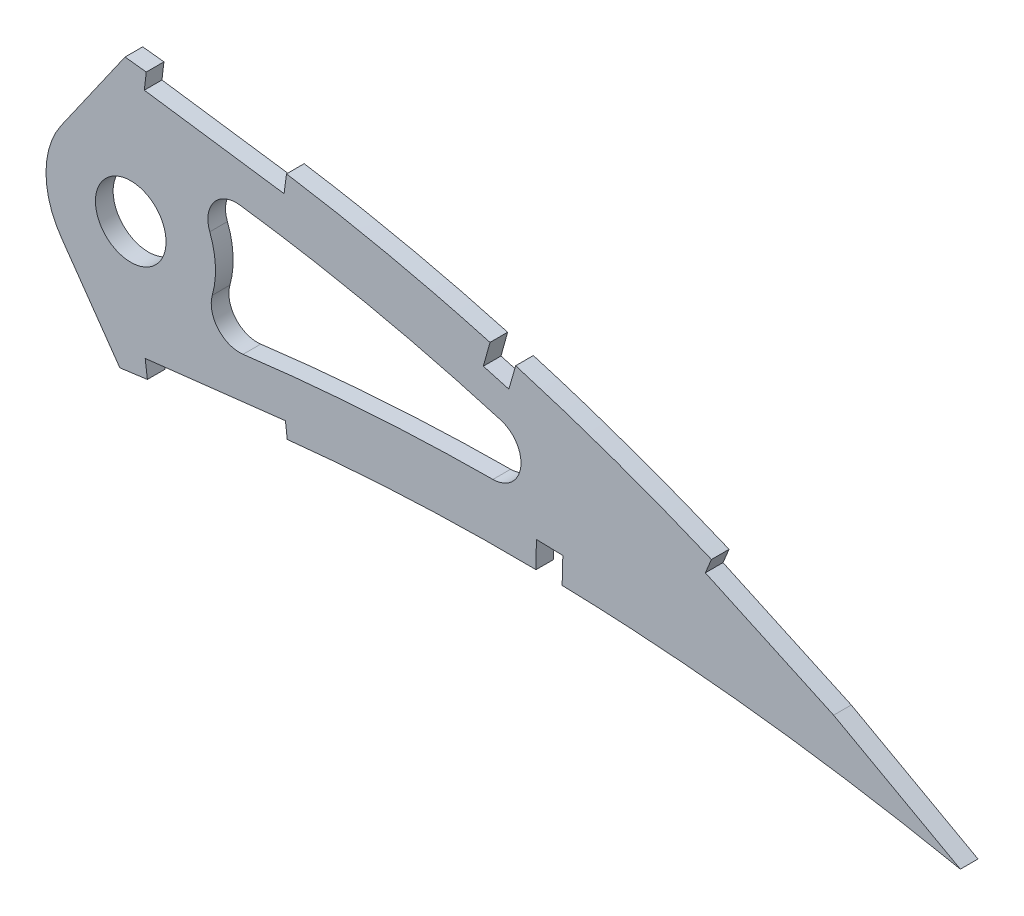
SolidWorks part; units mm, degrees
ref_plane "Front Plane" through (0, 0, 0) normal (0, 0, 1) x (1, 0, 0)
ref_plane "Top Plane" through (0, 0, 0) normal (0, 1, 0) x (1, 0, 0)
ref_plane "Right Plane" through (0, 0, 0) normal (1, 0, 0) x (0, 0, -1)
curve "Curve1"
  spline degree 3 poles (452.1031, 0.7048, 0) (452.0685, 0.7262, 0) (451.9301, 0.8117, 0) (451.6183, 1.003, 0) (451.099, 1.3216, 0) (450.372, 1.7653, 0) (449.438, 2.3329, 0) (448.2963, 3.0204, 0) (446.9478, 3.8257, 0) (445.3928, 4.7448, 0) (443.6314, 5.7736, 0) (441.6643, 6.9077, 0) (439.4916, 8.1409, 0) (437.1143, 9.468, 0) (434.5331, 10.8828, 0) (431.7485, 12.3789, 0) (428.7615, 13.9486, 0) (425.5733, 15.5853, 0) (422.1844, 17.2798, 0) (418.5964, 19.0251, 0) (414.8106, 20.8125, 0) (410.8282, 22.6325, 0) (406.6515, 24.4776, 0) (402.2816, 26.3365, 0) (397.7212, 28.201, 0) (392.972, 30.0605, 0) (388.0369, 31.9065, 0) (382.9178, 33.7272, 0) (377.6186, 35.5144, 0) (372.1418, 37.2567, 0) (366.4913, 38.9446, 0) (360.6704, 40.5671, 0) (354.684, 42.1159, 0) (348.5359, 43.5797, 0) (342.2312, 44.9487, 0) (335.775, 46.2147, 0) (329.1727, 47.3651, 0) (322.4425, 48.3989, 0) (315.6929, 49.2588, 0) (308.9571, 50.1023, 0) (302.2314, 50.8946, 0) (295.4235, 51.6533, 0) (288.5399, 52.3742, 0) (281.5875, 53.055, 0) (274.5733, 53.6928, 0) (267.5046, 54.2857, 0) (260.3883, 54.8303, 0) (253.2318, 55.3259, 0) (246.0422, 55.768, 0) (238.8272, 56.1563, 0) (231.5941, 56.4881, 0) (224.3504, 56.7611, 0) (217.1039, 56.9737, 0) (209.862, 57.1238, 0) (202.6326, 57.2105, 0) (195.4232, 57.2315, 0) (188.2416, 57.1863, 0) (181.0954, 57.0734, 0) (173.9924, 56.8912, 0) (166.9401, 56.6395, 0) (159.9462, 56.3182, 0) (153.0184, 55.9248, 0) (146.164, 55.4618, 0) (139.3909, 54.9271, 0) (132.7063, 54.3206, 0) (126.1174, 53.645, 0) (119.6314, 52.8983, 0) (113.2554, 52.0826, 0) (106.9962, 51.1996, 0) (100.8609, 50.2488, 0) (94.8561, 49.2329, 0) (88.9882, 48.153, 0) (83.2635, 47.0122, 0) (77.6882, 45.8109, 0) (72.2682, 44.5525, 0) (67.0092, 43.2395, 0) (61.9167, 41.874, 0) (56.9959, 40.4594, 0) (52.2519, 38.999, 0) (47.6902, 37.4943, 0) (43.3141, 35.951, 0) (39.1291, 34.3702, 0) (35.1384, 32.7568, 0) (31.3466, 31.113, 0) (27.7567, 29.4439, 0) (24.3726, 27.7512, 0) (21.1967, 26.0397, 0) (18.2324, 24.3122, 0) (15.4823, 22.5717, 0) (12.9477, 20.8227, 0) (10.632, 19.0664, 0) (8.5361, 17.307, 0) (6.6613, 15.5474, 0) (5.0102, 13.7886, 0) (3.5829, 12.0339, 0) (2.3811, 10.2847, 0) (1.4051, 8.5424, 0) (0.6571, 6.8085, 0) (0.1363, 5.084, 0) (-0.1488, 3.3712, 0) (-0.2197, 1.669, 0) (-0.0731, 0.5555, 0) (0, 0, 0) knots 0 0 0 0 0.000254 0.001015 0.002283 0.004057 0.006331 0.009105 0.012374 0.016134 0.02038 0.025106 0.030306 0.035972 0.0421 0.048678 0.055702 0.06316 0.071046 0.07935 0.088063 0.097176 0.106678 0.116562 0.126814 0.137428 0.148394 0.1597 0.171338 0.183298 0.19557 0.208144 0.221012 0.234162 0.247587 0.261277 0.275223 0.289414 0.303771 0.317689 0.331784 0.34604 0.360444 0.374983 0.38964 0.404403 0.419257 0.434187 0.449177 0.464215 0.479284 0.49437 0.509458 0.524532 0.539579 0.554583 0.56953 0.584403 0.599191 0.613877 0.628447 0.642889 0.657186 0.671326 0.685294 0.699078 0.712665 0.726043 0.739198 0.752118 0.764792 0.777208 0.789356 0.801224 0.812804 0.824083 0.835055 0.84571 0.856038 0.866034 0.875689 0.884998 0.893953 0.902553 0.910789 0.918661 0.926166 0.933303 0.940071 0.946475 0.952518 0.958205 0.963547 0.968557 0.97325 0.977651 0.981787 0.985694 0.989415 0.993001 0.996508 1 1 1 1
curve "Curve2"
  spline degree 3 poles (0, 0, 0) (0.1161, -0.5481, 0) (0.3488, -1.6467, 0) (0.9811, -3.2283, 0) (1.8173, -4.7487, 0) (2.8749, -6.2038, 0) (4.147, -7.5932, 0) (5.6306, -8.9184, 0) (7.3243, -10.1787, 0) (9.226, -11.3735, 0) (11.3328, -12.5041, 0) (13.6425, -13.5697, 0) (16.1528, -14.5701, 0) (18.8611, -15.5039, 0) (21.764, -16.3724, 0) (24.8588, -17.1737, 0) (28.1419, -17.9088, 0) (31.6103, -18.5759, 0) (35.26, -19.1755, 0) (39.0874, -19.7075, 0) (43.0885, -20.172, 0) (47.2594, -20.5682, 0) (51.596, -20.8969, 0) (56.0938, -21.1583, 0) (60.7487, -21.3533, 0) (65.556, -21.481, 0) (70.5112, -21.5436, 0) (75.6096, -21.5419, 0) (80.8464, -21.4754, 0) (86.2171, -21.3479, 0) (91.7164, -21.1586, 0) (97.3395, -20.9096, 0) (103.0813, -20.6036, 0) (108.9365, -20.2416, 0) (114.9002, -19.8251, 0) (120.967, -19.3576, 0) (127.1315, -18.8401, 0) (133.3883, -18.2757, 0) (139.7319, -17.6673, 0) (146.1567, -17.0167, 0) (152.6572, -16.327, 0) (159.2275, -15.6004, 0) (165.862, -14.8409, 0) (172.5546, -14.0497, 0) (179.2998, -13.2315, 0) (186.0911, -12.3877, 0) (192.923, -11.5217, 0) (199.7891, -10.6375, 0) (206.6832, -9.7349, 0) (213.5994, -8.8205, 0) (220.5311, -7.8935, 0) (227.4721, -6.9586, 0) (234.4161, -6.0188, 0) (241.3564, -5.0743, 0) (248.2868, -4.1291, 0) (255.2009, -3.1857, 0) (262.0918, -2.2442, 0) (268.9535, -1.3094, 0) (275.779, -0.3811, 0) (282.5619, 0.5389, 0) (289.2958, 1.4477, 0) (295.9744, 2.3443, 0) (302.5907, 3.228, 0) (309.138, 4.0992, 0) (315.5119, 4.9314, 0) (321.6955, 5.769, 0) (327.7099, 6.4556, 0) (333.6493, 7.0417, 0) (339.52, 7.5222, 0) (345.315, 7.9041, 0) (351.0275, 8.19, 0) (356.6509, 8.3839, 0) (362.1779, 8.4917, 0) (367.6017, 8.516, 0) (372.9148, 8.4647, 0) (378.1105, 8.3417, 0) (383.1813, 8.1528, 0) (388.1203, 7.9042, 0) (392.9205, 7.6027, 0) (397.5745, 7.2527, 0) (402.076, 6.8625, 0) (406.4179, 6.4377, 0) (410.5937, 5.9833, 0) (414.5972, 5.5086, 0) (418.4221, 5.0169, 0) (422.0625, 4.5163, 0) (425.5126, 4.0117, 0) (428.7669, 3.5097, 0) (431.8204, 3.015, 0) (434.6681, 2.5342, 0) (437.3055, 2.0718, 0) (439.7281, 1.6323, 0) (441.9324, 1.2212, 0) (443.9143, 0.8406, 0) (445.6709, 0.4968, 0) (447.199, 0.1913, 0) (448.4964, -0.0716, 0) (449.5609, -0.2909, 0) (450.3908, -0.463, 0) (450.9844, -0.5881, 0) (451.3411, -0.6626, 0) (451.4997, -0.6964, 0) (451.5393, -0.7048, 0) knots 0 0 0 0 0.003638 0.007293 0.011028 0.014901 0.018963 0.023258 0.027821 0.032679 0.037853 0.043362 0.049215 0.055422 0.061989 0.068918 0.076211 0.083868 0.091887 0.100266 0.109 0.118085 0.127515 0.137285 0.147388 0.157816 0.168563 0.179619 0.190977 0.202627 0.21456 0.226767 0.239236 0.251959 0.264924 0.27812 0.291536 0.30516 0.318981 0.332985 0.347163 0.361499 0.375981 0.390597 0.405333 0.420175 0.43511 0.450124 0.465203 0.480333 0.495501 0.51069 0.525887 0.541078 0.556247 0.571382 0.586466 0.601485 0.616424 0.631269 0.646007 0.660621 0.675098 0.689423 0.703582 0.716908 0.730009 0.742952 0.755726 0.76832 0.780724 0.792927 0.804916 0.816679 0.828204 0.839475 0.850481 0.861208 0.871639 0.881763 0.891564 0.901027 0.910139 0.918884 0.927249 0.935221 0.942785 0.949928 0.956638 0.962904 0.968712 0.974054 0.978918 0.983297 0.98718 0.990561 0.993433 0.995791 0.99763 0.998946 0.999737 1 1 1 1
sketch "Sketch1" plane through (0, 0, 0) normal (0, 0, 1) x (1, 0, 0)
  line L24 (452.1031, 0.7048) -> (456.094, -1.6764)
  line L25 (451.5393, -0.7048) -> (456.094, -1.6764)
  spline S2 degree 3 poles (-3866.0233, -1022.3851) (78.0891, 72.3921) (-8.7669, 21.1547) (0.9811, -3.2283) (1.8173, -4.7487) (2.8749, -6.2038) (4.147, -7.5932) (5.6306, -8.9184) (7.3243, -10.1787) (9.226, -11.3735) (11.3328, -12.5041) (13.6425, -13.5697) (16.1528, -14.5701) (18.8611, -15.5039) (21.764, -16.3724) (24.8588, -17.1737) (28.1419, -17.9088) (31.6103, -18.5759) (35.26, -19.1755) (39.0874, -19.7075) (43.0885, -20.172) (47.2594, -20.5682) (51.596, -20.8969) (56.0938, -21.1583) (60.7487, -21.3533) (65.556, -21.481) (70.5112, -21.5436) (75.6096, -21.5419) (80.8464, -21.4754) (86.2171, -21.3479) (91.7164, -21.1586) (97.3395, -20.9096) (103.0813, -20.6036) (108.9365, -20.2416) (114.9002, -19.8251) (120.967, -19.3576) (127.1315, -18.8401) (133.3883, -18.2757) (139.7319, -17.6673) (146.1567, -17.0167) (152.6572, -16.327) (159.2275, -15.6004) (165.862, -14.8409) (172.5546, -14.0497) (179.2998, -13.2315) (186.0911, -12.3877) (192.923, -11.5217) (199.7891, -10.6375) (206.6832, -9.7349) (213.5994, -8.8205) (220.5311, -7.8935) (227.4721, -6.9586) (234.4161, -6.0188) (241.3564, -5.0743) (248.2868, -4.1291) (255.2009, -3.1857) (262.0918, -2.2442) (268.9535, -1.3094) (275.779, -0.3811) (282.5619, 0.5389) (289.2958, 1.4477) (295.9744, 2.3443) (302.5907, 3.228) (309.138, 4.0992) (315.5119, 4.9314) (321.6955, 5.769) (327.7099, 6.4556) (333.6493, 7.0417) (339.52, 7.5222) (345.315, 7.9041) (351.0275, 8.19) (356.6509, 8.3839) (362.1779, 8.4917) (367.6017, 8.516) (372.9148, 8.4647) (378.1105, 8.3417) (383.1813, 8.1528) (388.1203, 7.9042) (392.9205, 7.6027) (397.5745, 7.2527) (402.076, 6.8625) (406.4179, 6.4377) (410.5937, 5.9833) (414.5972, 5.5086) (418.4221, 5.0169) (422.0625, 4.5163) (425.5126, 4.0117) (428.7669, 3.5097) (431.8204, 3.015) (434.6681, 2.5342) (437.3055, 2.0718) (439.7281, 1.6323) (441.9324, 1.2212) (443.9143, 0.8406) (445.6709, 0.4968) (447.199, 0.1913) (448.4964, -0.0716) (449.5609, -0.2909) (450.3908, -0.463) (450.9844, -0.5881) (469.101, -4.3694) (485.1398, -16.9975) (1332.023, 3899.5324) knots -0.15899 -0.15899 -0.15899 -0.15899 0.003638 0.007293 0.011028 0.014901 0.018963 0.023258 0.027821 0.032679 0.037853 0.043362 0.049215 0.055422 0.061989 0.068918 0.076211 0.083868 0.091887 0.100266 0.109 0.118085 0.127515 0.137285 0.147388 0.157816 0.168563 0.179619 0.190977 0.202627 0.21456 0.226767 0.239236 0.251959 0.264924 0.27812 0.291536 0.30516 0.318981 0.332985 0.347163 0.361499 0.375981 0.390597 0.405333 0.420175 0.43511 0.450124 0.465203 0.480333 0.495501 0.51069 0.525887 0.541078 0.556247 0.571382 0.586466 0.601485 0.616424 0.631269 0.646007 0.660621 0.675098 0.689423 0.703582 0.716908 0.730009 0.742952 0.755726 0.76832 0.780724 0.792927 0.804916 0.816679 0.828204 0.839475 0.850481 0.861208 0.871639 0.881763 0.891564 0.901027 0.910139 0.918884 0.927249 0.935221 0.942785 0.949928 0.956638 0.962904 0.968712 0.974054 0.978918 0.983297 0.98718 0.990561 0.993433 0.995791 0.99763 0.998946 0.999737 1.118004 1.118004 1.118004 1.118004 only from (0, 0) to (451.5393, -0.7048) construction
  spline S3 degree 3 poles (2601.1012, 3372.9476) (482.3924, -27.4342) (469.2292, -9.7993) (451.6183, 1.003) (451.099, 1.3216) (450.372, 1.7653) (449.438, 2.3329) (448.2963, 3.0204) (446.9478, 3.8257) (445.3928, 4.7448) (443.6314, 5.7736) (441.6643, 6.9077) (439.4916, 8.1409) (437.1143, 9.468) (434.5331, 10.8828) (431.7485, 12.3789) (428.7615, 13.9486) (425.5733, 15.5853) (422.1844, 17.2798) (418.5964, 19.0251) (414.8106, 20.8125) (410.8282, 22.6325) (406.6515, 24.4776) (402.2816, 26.3365) (397.7212, 28.201) (392.972, 30.0605) (388.0369, 31.9065) (382.9178, 33.7272) (377.6186, 35.5144) (372.1418, 37.2567) (366.4913, 38.9446) (360.6704, 40.5671) (354.684, 42.1159) (348.5359, 43.5797) (342.2312, 44.9487) (335.775, 46.2147) (329.1727, 47.3651) (322.4425, 48.3989) (315.6929, 49.2588) (308.9571, 50.1023) (302.2314, 50.8946) (295.4235, 51.6533) (288.5399, 52.3742) (281.5875, 53.055) (274.5733, 53.6928) (267.5046, 54.2857) (260.3883, 54.8303) (253.2318, 55.3259) (246.0422, 55.768) (238.8272, 56.1563) (231.5941, 56.4881) (224.3504, 56.7611) (217.1039, 56.9737) (209.862, 57.1238) (202.6326, 57.2105) (195.4232, 57.2315) (188.2416, 57.1863) (181.0954, 57.0734) (173.9924, 56.8912) (166.9401, 56.6395) (159.9462, 56.3182) (153.0184, 55.9248) (146.164, 55.4618) (139.3909, 54.9271) (132.7063, 54.3206) (126.1174, 53.645) (119.6314, 52.8983) (113.2554, 52.0826) (106.9962, 51.1996) (100.8609, 50.2488) (94.8561, 49.2329) (88.9882, 48.153) (83.2635, 47.0122) (77.6882, 45.8109) (72.2682, 44.5525) (67.0092, 43.2395) (61.9167, 41.874) (56.9959, 40.4594) (52.2519, 38.999) (47.6902, 37.4943) (43.3141, 35.951) (39.1291, 34.3702) (35.1384, 32.7568) (31.3466, 31.113) (27.7567, 29.4439) (24.3726, 27.7512) (21.1967, 26.0397) (18.2324, 24.3122) (15.4823, 22.5717) (12.9477, 20.8227) (10.632, 19.0664) (8.5361, 17.307) (6.6613, 15.5474) (5.0102, 13.7886) (3.5829, 12.0339) (2.3811, 10.2847) (1.4051, 8.5424) (0.6571, 6.8085) (0.1363, 5.084) (-0.1488, 3.3712) (-1.2405, -22.8207) (97.9167, -42.1829) (-3985.8979, -321.9579) knots -0.126667 -0.126667 -0.126667 -0.126667 0.000254 0.001015 0.002283 0.004057 0.006331 0.009105 0.012374 0.016134 0.02038 0.025106 0.030306 0.035972 0.0421 0.048678 0.055702 0.06316 0.071046 0.07935 0.088063 0.097176 0.106678 0.116562 0.126814 0.137428 0.148394 0.1597 0.171338 0.183298 0.19557 0.208144 0.221012 0.234162 0.247587 0.261277 0.275223 0.289414 0.303771 0.317689 0.331784 0.34604 0.360444 0.374983 0.38964 0.404403 0.419257 0.434187 0.449177 0.464215 0.479284 0.49437 0.509458 0.524532 0.539579 0.554583 0.56953 0.584403 0.599191 0.613877 0.628447 0.642889 0.657186 0.671326 0.685294 0.699078 0.712665 0.726043 0.739198 0.752118 0.764792 0.777208 0.789356 0.801224 0.812804 0.824083 0.835055 0.84571 0.856038 0.866034 0.875689 0.884998 0.893953 0.902553 0.910789 0.918661 0.926166 0.933303 0.940071 0.946475 0.952518 0.958205 0.963547 0.968557 0.97325 0.977651 0.981787 0.985694 0.989415 0.993001 0.996508 1.15228 1.15228 1.15228 1.15228 only from (452.1031, 0.7048) to (0, 0) construction
  spline S4 degree 3 poles (0, 0) (0.1161, -0.5481) (0.3488, -1.6467) (0.9811, -3.2283) (1.8173, -4.7487) (2.8749, -6.2038) (4.147, -7.5932) (5.6306, -8.9184) (7.3243, -10.1787) (9.226, -11.3735) (11.3328, -12.5041) (13.6425, -13.5697) (16.1528, -14.5701) (18.8611, -15.5039) (21.764, -16.3724) (24.8588, -17.1737) (28.1419, -17.9088) (31.6103, -18.5759) (35.26, -19.1755) (39.0874, -19.7075) (43.0885, -20.172) (47.2594, -20.5682) (51.596, -20.8969) (56.0938, -21.1583) (60.7487, -21.3533) (65.556, -21.481) (70.5112, -21.5436) (75.6096, -21.5419) (80.8464, -21.4754) (86.2171, -21.3479) (91.7164, -21.1586) (97.3395, -20.9096) (103.0813, -20.6036) (108.9365, -20.2416) (114.9002, -19.8251) (120.967, -19.3576) (127.1315, -18.8401) (133.3883, -18.2757) (139.7319, -17.6673) (146.1567, -17.0167) (152.6572, -16.327) (159.2275, -15.6004) (165.862, -14.8409) (172.5546, -14.0497) (179.2998, -13.2315) (186.0911, -12.3877) (192.923, -11.5217) (199.7891, -10.6375) (206.6832, -9.7349) (213.5994, -8.8205) (220.5311, -7.8935) (227.4721, -6.9586) (234.4161, -6.0188) (241.3564, -5.0743) (248.2868, -4.1291) (255.2009, -3.1857) (262.0918, -2.2442) (268.9535, -1.3094) (275.779, -0.3811) (282.5619, 0.5389) (289.2958, 1.4477) (295.9744, 2.3443) (302.5907, 3.228) (309.138, 4.0992) (315.5119, 4.9314) (321.6955, 5.769) (327.7099, 6.4556) (333.6493, 7.0417) (339.52, 7.5222) (345.315, 7.9041) (351.0275, 8.19) (356.6509, 8.3839) (362.1779, 8.4917) (367.6017, 8.516) (372.9148, 8.4647) (378.1105, 8.3417) (383.1813, 8.1528) (388.1203, 7.9042) (392.9205, 7.6027) (397.5745, 7.2527) (402.076, 6.8625) (406.4179, 6.4377) (410.5937, 5.9833) (414.5972, 5.5086) (418.4221, 5.0169) (422.0625, 4.5163) (425.5126, 4.0117) (428.7669, 3.5097) (431.8204, 3.015) (434.6681, 2.5342) (437.3055, 2.0718) (439.7281, 1.6323) (441.9324, 1.2212) (443.9143, 0.8406) (445.6709, 0.4968) (447.199, 0.1913) (448.4964, -0.0716) (449.5609, -0.2909) (450.3908, -0.463) (450.9844, -0.5881) (451.3411, -0.6626) (451.4997, -0.6964) (451.5393, -0.7048) knots 0 0 0 0 0.003638 0.007293 0.011028 0.014901 0.018963 0.023258 0.027821 0.032679 0.037853 0.043362 0.049215 0.055422 0.061989 0.068918 0.076211 0.083868 0.091887 0.100266 0.109 0.118085 0.127515 0.137285 0.147388 0.157816 0.168563 0.179619 0.190977 0.202627 0.21456 0.226767 0.239236 0.251959 0.264924 0.27812 0.291536 0.30516 0.318981 0.332985 0.347163 0.361499 0.375981 0.390597 0.405333 0.420175 0.43511 0.450124 0.465203 0.480333 0.495501 0.51069 0.525887 0.541078 0.556247 0.571382 0.586466 0.601485 0.616424 0.631269 0.646007 0.660621 0.675098 0.689423 0.703582 0.716908 0.730009 0.742952 0.755726 0.76832 0.780724 0.792927 0.804916 0.816679 0.828204 0.839475 0.850481 0.861208 0.871639 0.881763 0.891564 0.901027 0.910139 0.918884 0.927249 0.935221 0.942785 0.949928 0.956638 0.962904 0.968712 0.974054 0.978918 0.983297 0.98718 0.990561 0.993433 0.995791 0.99763 0.998946 0.999737 1 1 1 1
  spline S5 degree 3 poles (452.1031, 0.7048) (452.0685, 0.7262) (451.9301, 0.8117) (451.6183, 1.003) (451.099, 1.3216) (450.372, 1.7653) (449.438, 2.3329) (448.2963, 3.0204) (446.9478, 3.8257) (445.3928, 4.7448) (443.6314, 5.7736) (441.6643, 6.9077) (439.4916, 8.1409) (437.1143, 9.468) (434.5331, 10.8828) (431.7485, 12.3789) (428.7615, 13.9486) (425.5733, 15.5853) (422.1844, 17.2798) (418.5964, 19.0251) (414.8106, 20.8125) (410.8282, 22.6325) (406.6515, 24.4776) (402.2816, 26.3365) (397.7212, 28.201) (392.972, 30.0605) (388.0369, 31.9065) (382.9178, 33.7272) (377.6186, 35.5144) (372.1418, 37.2567) (366.4913, 38.9446) (360.6704, 40.5671) (354.684, 42.1159) (348.5359, 43.5797) (342.2312, 44.9487) (335.775, 46.2147) (329.1727, 47.3651) (322.4425, 48.3989) (315.6929, 49.2588) (308.9571, 50.1023) (302.2314, 50.8946) (295.4235, 51.6533) (288.5399, 52.3742) (281.5875, 53.055) (274.5733, 53.6928) (267.5046, 54.2857) (260.3883, 54.8303) (253.2318, 55.3259) (246.0422, 55.768) (238.8272, 56.1563) (231.5941, 56.4881) (224.3504, 56.7611) (217.1039, 56.9737) (209.862, 57.1238) (202.6326, 57.2105) (195.4232, 57.2315) (188.2416, 57.1863) (181.0954, 57.0734) (173.9924, 56.8912) (166.9401, 56.6395) (159.9462, 56.3182) (153.0184, 55.9248) (146.164, 55.4618) (139.3909, 54.9271) (132.7063, 54.3206) (126.1174, 53.645) (119.6314, 52.8983) (113.2554, 52.0826) (106.9962, 51.1996) (100.8609, 50.2488) (94.8561, 49.2329) (88.9882, 48.153) (83.2635, 47.0122) (77.6882, 45.8109) (72.2682, 44.5525) (67.0092, 43.2395) (61.9167, 41.874) (56.9959, 40.4594) (52.2519, 38.999) (47.6902, 37.4943) (43.3141, 35.951) (39.1291, 34.3702) (35.1384, 32.7568) (31.3466, 31.113) (27.7567, 29.4439) (24.3726, 27.7512) (21.1967, 26.0397) (18.2324, 24.3122) (15.4823, 22.5717) (12.9477, 20.8227) (10.632, 19.0664) (8.5361, 17.307) (6.6613, 15.5474) (5.0102, 13.7886) (3.5829, 12.0339) (2.3811, 10.2847) (1.4051, 8.5424) (0.6571, 6.8085) (0.1363, 5.084) (-0.1488, 3.3712) (-0.2197, 1.669) (-0.0731, 0.5555) (0, 0) knots 0 0 0 0 0.000254 0.001015 0.002283 0.004057 0.006331 0.009105 0.012374 0.016134 0.02038 0.025106 0.030306 0.035972 0.0421 0.048678 0.055702 0.06316 0.071046 0.07935 0.088063 0.097176 0.106678 0.116562 0.126814 0.137428 0.148394 0.1597 0.171338 0.183298 0.19557 0.208144 0.221012 0.234162 0.247587 0.261277 0.275223 0.289414 0.303771 0.317689 0.331784 0.34604 0.360444 0.374983 0.38964 0.404403 0.419257 0.434187 0.449177 0.464215 0.479284 0.49437 0.509458 0.524532 0.539579 0.554583 0.56953 0.584403 0.599191 0.613877 0.628447 0.642889 0.657186 0.671326 0.685294 0.699078 0.712665 0.726043 0.739198 0.752118 0.764792 0.777208 0.789356 0.801224 0.812804 0.824083 0.835055 0.84571 0.856038 0.866034 0.875689 0.884998 0.893953 0.902553 0.910789 0.918661 0.926166 0.933303 0.940071 0.946475 0.952518 0.958205 0.963547 0.968557 0.97325 0.977651 0.981787 0.985694 0.989415 0.993001 0.996508 1 1 1 1
extrude "Boss-Extrude1" add sketch "Sketch1" along normal blind 3.175
sketch "Sketch3" plane through (0, 0, 0) normal (0, 0, -1) x (-1, 0, 0)
  circle A1 centre (-299.0384, 26.2554) radius 6.35
extrude "Cut-Extrude2" cut sketch "Sketch3" against normal blind 7.62
sketch "Sketch4" plane through (0, 0, 3.175) normal (0, 0, 1) x (1, 0, 0)
  line L0 (286.5546, 34.9967) -> (298.0139, 51.3624)
  line L1 (286.5546, 17.5141) -> (297.0741, 2.4907)
  line L2 (299.0384, 26.2554) -> (339.6276, 26.2554)
  circle A0 centre (299.0384, 26.2554) radius 6.35 construction
  circle A1 centre (299.0384, 26.2554) radius 6.35
  circle A2 centre (299.0384, 26.2554) radius 15.24
  spline S0 degree 3 poles (-2902.3793, -755.52) (63.6454, 63.6466) (-7.9338, 19.0709) (0.9811, -3.2283) (1.8173, -4.7487) (2.8749, -6.2038) (4.147, -7.5932) (5.6306, -8.9184) (7.3243, -10.1787) (9.226, -11.3735) (11.3328, -12.5041) (13.6425, -13.5697) (16.1528, -14.5701) (18.8611, -15.5039) (21.764, -16.3724) (24.8588, -17.1737) (28.1419, -17.9088) (31.6103, -18.5759) (35.26, -19.1755) (39.0874, -19.7075) (43.0885, -20.172) (47.2594, -20.5682) (51.596, -20.8969) (56.0938, -21.1583) (60.7487, -21.3533) (65.556, -21.481) (70.5112, -21.5436) (75.6096, -21.5419) (80.8464, -21.4754) (86.2171, -21.3479) (91.7164, -21.1586) (97.3395, -20.9096) (103.0813, -20.6036) (108.9365, -20.2416) (114.9002, -19.8251) (120.967, -19.3576) (127.1315, -18.8401) (133.3883, -18.2757) (139.7319, -17.6673) (146.1567, -17.0167) (152.6572, -16.327) (159.2275, -15.6004) (165.862, -14.8409) (172.5546, -14.0497) (179.2998, -13.2315) (186.0911, -12.3877) (192.923, -11.5217) (199.7891, -10.6375) (206.6832, -9.7349) (213.5994, -8.8205) (220.5311, -7.8935) (227.4721, -6.9586) (234.4161, -6.0188) (241.3564, -5.0743) (248.2868, -4.1291) (255.2009, -3.1857) (262.0918, -2.2442) (268.9535, -1.3094) (275.779, -0.3811) (282.5619, 0.5389) (289.2958, 1.4477) (295.9744, 2.3443) (302.5907, 3.228) (309.138, 4.0992) (315.5119, 4.9314) (321.6955, 5.769) (327.7099, 6.4556) (333.6493, 7.0417) (339.52, 7.5222) (345.315, 7.9041) (351.0275, 8.19) (356.6509, 8.3839) (362.1779, 8.4917) (367.6017, 8.516) (372.9148, 8.4647) (378.1105, 8.3417) (383.1813, 8.1528) (388.1203, 7.9042) (392.9205, 7.6027) (397.5745, 7.2527) (402.076, 6.8625) (406.4179, 6.4377) (410.5937, 5.9833) (414.5972, 5.5086) (418.4221, 5.0169) (422.0625, 4.5163) (425.5126, 4.0117) (428.7669, 3.5097) (431.8204, 3.015) (434.6681, 2.5342) (437.3055, 2.0718) (439.7281, 1.6323) (441.9324, 1.2212) (443.9143, 0.8406) (445.6709, 0.4968) (447.199, 0.1913) (448.4964, -0.0716) (449.5609, -0.2909) (450.3908, -0.463) (450.9844, -0.5881) (467.4773, -4.0305) (482.2176, -14.7818) (1120.3699, 2922.8002) knots -0.14446 -0.14446 -0.14446 -0.14446 0.003638 0.007293 0.011028 0.014901 0.018963 0.023258 0.027821 0.032679 0.037853 0.043362 0.049215 0.055422 0.061989 0.068918 0.076211 0.083868 0.091887 0.100266 0.109 0.118085 0.127515 0.137285 0.147388 0.157816 0.168563 0.179619 0.190977 0.202627 0.21456 0.226767 0.239236 0.251959 0.264924 0.27812 0.291536 0.30516 0.318981 0.332985 0.347163 0.361499 0.375981 0.390597 0.405333 0.420175 0.43511 0.450124 0.465203 0.480333 0.495501 0.51069 0.525887 0.541078 0.556247 0.571382 0.586466 0.601485 0.616424 0.631269 0.646007 0.660621 0.675098 0.689423 0.703582 0.716908 0.730009 0.742952 0.755726 0.76832 0.780724 0.792927 0.804916 0.816679 0.828204 0.839475 0.850481 0.861208 0.871639 0.881763 0.891564 0.901027 0.910139 0.918884 0.927249 0.935221 0.942785 0.949928 0.956638 0.962904 0.968712 0.974054 0.978918 0.983297 0.98718 0.990561 0.993433 0.995791 0.99763 0.998946 0.999737 1.107215 1.107215 1.107215 1.107215 only from (0, 0) to (451.5393, -0.7048) construction
  spline S1 degree 3 poles (2072.0463, 2524.7843) (479.969, -24.2918) (467.6474, -8.829) (451.6183, 1.003) (451.099, 1.3216) (450.372, 1.7653) (449.438, 2.3329) (448.2963, 3.0204) (446.9478, 3.8257) (445.3928, 4.7448) (443.6314, 5.7736) (441.6643, 6.9077) (439.4916, 8.1409) (437.1143, 9.468) (434.5331, 10.8828) (431.7485, 12.3789) (428.7615, 13.9486) (425.5733, 15.5853) (422.1844, 17.2798) (418.5964, 19.0251) (414.8106, 20.8125) (410.8282, 22.6325) (406.6515, 24.4776) (402.2816, 26.3365) (397.7212, 28.201) (392.972, 30.0605) (388.0369, 31.9065) (382.9178, 33.7272) (377.6186, 35.5144) (372.1418, 37.2567) (366.4913, 38.9446) (360.6704, 40.5671) (354.684, 42.1159) (348.5359, 43.5797) (342.2312, 44.9487) (335.775, 46.2147) (329.1727, 47.3651) (322.4425, 48.3989) (315.6929, 49.2588) (308.9571, 50.1023) (302.2314, 50.8946) (295.4235, 51.6533) (288.5399, 52.3742) (281.5875, 53.055) (274.5733, 53.6928) (267.5046, 54.2857) (260.3883, 54.8303) (253.2318, 55.3259) (246.0422, 55.768) (238.8272, 56.1563) (231.5941, 56.4881) (224.3504, 56.7611) (217.1039, 56.9737) (209.862, 57.1238) (202.6326, 57.2105) (195.4232, 57.2315) (188.2416, 57.1863) (181.0954, 57.0734) (173.9924, 56.8912) (166.9401, 56.6395) (159.9462, 56.3182) (153.0184, 55.9248) (146.164, 55.4618) (139.3909, 54.9271) (132.7063, 54.3206) (126.1174, 53.645) (119.6314, 52.8983) (113.2554, 52.0826) (106.9962, 51.1996) (100.8609, 50.2488) (94.8561, 49.2329) (88.9882, 48.153) (83.2635, 47.0122) (77.6882, 45.8109) (72.2682, 44.5525) (67.0092, 43.2395) (61.9167, 41.874) (56.9959, 40.4594) (52.2519, 38.999) (47.6902, 37.4943) (43.3141, 35.951) (39.1291, 34.3702) (35.1384, 32.7568) (31.3466, 31.113) (27.7567, 29.4439) (24.3726, 27.7512) (21.1967, 26.0397) (18.2324, 24.3122) (15.4823, 22.5717) (12.9477, 20.8227) (10.632, 19.0664) (8.5361, 17.307) (6.6613, 15.5474) (5.0102, 13.7886) (3.5829, 12.0339) (2.3811, 10.2847) (1.4051, 8.5424) (0.6571, 6.8085) (0.1363, 5.084) (-0.1488, 3.3712) (-1.1473, -20.5831) (81.3582, -38.7525) (-2988.6181, -253.0424) knots -0.115084 -0.115084 -0.115084 -0.115084 0.000254 0.001015 0.002283 0.004057 0.006331 0.009105 0.012374 0.016134 0.02038 0.025106 0.030306 0.035972 0.0421 0.048678 0.055702 0.06316 0.071046 0.07935 0.088063 0.097176 0.106678 0.116562 0.126814 0.137428 0.148394 0.1597 0.171338 0.183298 0.19557 0.208144 0.221012 0.234162 0.247587 0.261277 0.275223 0.289414 0.303771 0.317689 0.331784 0.34604 0.360444 0.374983 0.38964 0.404403 0.419257 0.434187 0.449177 0.464215 0.479284 0.49437 0.509458 0.524532 0.539579 0.554583 0.56953 0.584403 0.599191 0.613877 0.628447 0.642889 0.657186 0.671326 0.685294 0.699078 0.712665 0.726043 0.739198 0.752118 0.764792 0.777208 0.789356 0.801224 0.812804 0.824083 0.835055 0.84571 0.856038 0.866034 0.875689 0.884998 0.893953 0.902553 0.910789 0.918661 0.926166 0.933303 0.940071 0.946475 0.952518 0.958205 0.963547 0.968557 0.97325 0.977651 0.981787 0.985694 0.989415 0.993001 0.996508 1.138367 1.138367 1.138367 1.138367 only from (452.1031, 0.7048) to (0, 0) construction
  spline S2 degree 3 poles (168.2219, -14.5606) (169.6601, -14.3914) (173.3479, -13.9535) (179.2998, -13.2315) (186.0911, -12.3877) (192.923, -11.5217) (199.7891, -10.6375) (206.6832, -9.7349) (213.5994, -8.8205) (220.5311, -7.8935) (227.4721, -6.9586) (234.4161, -6.0188) (241.3564, -5.0743) (248.2868, -4.1291) (255.2009, -3.1857) (262.0918, -2.2442) (268.9535, -1.3094) (275.779, -0.3811) (282.5619, 0.5389) (289.2958, 1.4477) (295.9744, 2.3443) (302.5907, 3.228) (309.138, 4.0992) (315.5119, 4.9314) (321.6955, 5.769) (327.7099, 6.4556) (333.6493, 7.0417) (339.52, 7.5222) (345.315, 7.9041) (351.0275, 8.19) (356.6509, 8.3839) (362.1779, 8.4917) (367.6017, 8.516) (372.9148, 8.4647) (378.1105, 8.3417) (383.1813, 8.1528) (388.1203, 7.9042) (392.9205, 7.6027) (397.5745, 7.2527) (402.076, 6.8625) (406.4179, 6.4377) (410.5937, 5.9833) (414.5972, 5.5086) (418.4221, 5.0169) (422.0625, 4.5163) (425.5126, 4.0117) (428.7669, 3.5097) (431.8204, 3.015) (434.6681, 2.5342) (437.3055, 2.0718) (439.7281, 1.6323) (441.9324, 1.2212) (443.9143, 0.8406) (445.6709, 0.4968) (447.199, 0.1913) (448.4964, -0.0716) (449.5609, -0.2909) (450.3908, -0.463) (450.9844, -0.5881) (451.3411, -0.6626) (451.4997, -0.6964) (451.5393, -0.7048) knots 0.381178 0.381178 0.381178 0.381178 0.390597 0.405333 0.420175 0.43511 0.450124 0.465203 0.480333 0.495501 0.51069 0.525887 0.541078 0.556247 0.571382 0.586466 0.601485 0.616424 0.631269 0.646007 0.660621 0.675098 0.689423 0.703582 0.716908 0.730009 0.742952 0.755726 0.76832 0.780724 0.792927 0.804916 0.816679 0.828204 0.839475 0.850481 0.861208 0.871639 0.881763 0.891564 0.901027 0.910139 0.918884 0.927249 0.935221 0.942785 0.949928 0.956638 0.962904 0.968712 0.974054 0.978918 0.983297 0.98718 0.990561 0.993433 0.995791 0.99763 0.998946 0.999737 1 1 1 1
  spline S3 degree 3 poles (452.1031, 0.7048) (452.0685, 0.7262) (451.9301, 0.8117) (451.6183, 1.003) (451.099, 1.3216) (450.372, 1.7653) (449.438, 2.3329) (448.2963, 3.0204) (446.9478, 3.8257) (445.3928, 4.7448) (443.6314, 5.7736) (441.6643, 6.9077) (439.4916, 8.1409) (437.1143, 9.468) (434.5331, 10.8828) (431.7485, 12.3789) (428.7615, 13.9486) (425.5733, 15.5853) (422.1844, 17.2798) (418.5964, 19.0251) (414.8106, 20.8125) (410.8282, 22.6325) (406.6515, 24.4776) (402.2816, 26.3365) (397.7212, 28.201) (392.972, 30.0605) (388.0369, 31.9065) (382.9178, 33.7272) (377.6186, 35.5144) (372.1418, 37.2567) (366.4913, 38.9446) (360.6704, 40.5671) (354.684, 42.1159) (348.5359, 43.5797) (342.2312, 44.9487) (335.775, 46.2147) (329.1727, 47.3651) (322.4425, 48.3989) (315.6929, 49.2588) (308.9571, 50.1023) (302.2314, 50.8946) (295.4235, 51.6533) (288.5399, 52.3742) (281.5875, 53.055) (274.5733, 53.6928) (267.5046, 54.2857) (260.3883, 54.8303) (253.2318, 55.3259) (246.0422, 55.768) (238.8272, 56.1563) (231.5941, 56.4881) (224.3504, 56.7611) (217.1039, 56.9737) (209.862, 57.1238) (202.6326, 57.2105) (195.4232, 57.2315) (188.2416, 57.1863) (181.0954, 57.0734) (173.9924, 56.8912) (166.9401, 56.6395) (159.9462, 56.3182) (154.9124, 56.0324) (152.2104, 55.8618) (151.8175, 55.8367) knots 0 0 0 0 0.000254 0.001015 0.002283 0.004057 0.006331 0.009105 0.012374 0.016134 0.02038 0.025106 0.030306 0.035972 0.0421 0.048678 0.055702 0.06316 0.071046 0.07935 0.088063 0.097176 0.106678 0.116562 0.126814 0.137428 0.148394 0.1597 0.171338 0.183298 0.19557 0.208144 0.221012 0.234162 0.247587 0.261277 0.275223 0.289414 0.303771 0.317689 0.331784 0.34604 0.360444 0.374983 0.38964 0.404403 0.419257 0.434187 0.449177 0.464215 0.479284 0.49437 0.509458 0.524532 0.539579 0.554583 0.56953 0.584403 0.599191 0.613877 0.628447 0.642889 0.645346 0.645346 0.645346 0.645346
  spline S4 degree 3 poles (151.8175, 55.8367) (149.9244, 55.7154) (145.7716, 55.4308) (139.3909, 54.9271) (132.7063, 54.3206) (126.1174, 53.645) (119.6314, 52.8983) (113.2554, 52.0826) (106.9962, 51.1996) (100.8609, 50.2488) (94.8561, 49.2329) (88.9882, 48.153) (83.2635, 47.0122) (77.6882, 45.8109) (72.2682, 44.5525) (67.0092, 43.2395) (61.9167, 41.874) (56.9959, 40.4594) (52.2519, 38.999) (47.6902, 37.4943) (43.3141, 35.951) (39.1291, 34.3702) (35.1384, 32.7568) (31.3466, 31.113) (27.7567, 29.4439) (24.3726, 27.7512) (21.1967, 26.0397) (18.2324, 24.3122) (15.4823, 22.5717) (12.9477, 20.8227) (10.632, 19.0664) (8.5361, 17.307) (6.6613, 15.5474) (5.0102, 13.7886) (3.5829, 12.0339) (2.3811, 10.2847) (1.4051, 8.5424) (0.6571, 6.8085) (0.1363, 5.084) (-0.1488, 3.3712) (-0.2197, 1.669) (-0.0731, 0.5555) (0, 0) knots 0.645346 0.645346 0.645346 0.645346 0.657186 0.671326 0.685294 0.699078 0.712665 0.726043 0.739198 0.752118 0.764792 0.777208 0.789356 0.801224 0.812804 0.824083 0.835055 0.84571 0.856038 0.866034 0.875689 0.884998 0.893953 0.902553 0.910789 0.918661 0.926166 0.933303 0.940071 0.946475 0.952518 0.958205 0.963547 0.968557 0.97325 0.977651 0.981787 0.985694 0.989415 0.993001 0.996508 1 1 1 1 construction
  spline S5 degree 3 poles (0, 0) (0.1161, -0.5481) (0.3488, -1.6467) (0.9811, -3.2283) (1.8173, -4.7487) (2.8749, -6.2038) (4.147, -7.5932) (5.6306, -8.9184) (7.3243, -10.1787) (9.226, -11.3735) (11.3328, -12.5041) (13.6425, -13.5697) (16.1528, -14.5701) (18.8611, -15.5039) (21.764, -16.3724) (24.8588, -17.1737) (28.1419, -17.9088) (31.6103, -18.5759) (35.26, -19.1755) (39.0874, -19.7075) (43.0885, -20.172) (47.2594, -20.5682) (51.596, -20.8969) (56.0938, -21.1583) (60.7487, -21.3533) (65.556, -21.481) (70.5112, -21.5436) (75.6096, -21.5419) (80.8464, -21.4754) (86.2171, -21.3479) (91.7164, -21.1586) (97.3395, -20.9096) (103.0813, -20.6036) (108.9365, -20.2416) (114.9002, -19.8251) (120.967, -19.3576) (127.1315, -18.8401) (133.3883, -18.2757) (139.7319, -17.6673) (146.1567, -17.0167) (152.6572, -16.327) (159.2275, -15.6004) (164.4232, -15.0056) (167.4283, -14.654) (168.2219, -14.5606) knots 0 0 0 0 0.003638 0.007293 0.011028 0.014901 0.018963 0.023258 0.027821 0.032679 0.037853 0.043362 0.049215 0.055422 0.061989 0.068918 0.076211 0.083868 0.091887 0.100266 0.109 0.118085 0.127515 0.137285 0.147388 0.157816 0.168563 0.179619 0.190977 0.202627 0.21456 0.226767 0.239236 0.251959 0.264924 0.27812 0.291536 0.30516 0.318981 0.332985 0.347163 0.361499 0.375981 0.381178 0.381178 0.381178 0.381178 construction
  spline S7 degree 1 poles (446.7634, -7.9388) (152.467, 45.6974) knots 0 0 1 1 construction
  spline S8 degree 3 poles (446.7634, -7.9388) (446.6007, -7.8383) (446.2797, -7.6414) (445.5971, -7.2229) (444.4249, -6.5084) (442.0753, -5.092) (437.3308, -2.2949) (427.7564, 3.0991) (408.1848, 13.1134) (384.9529, 22.6556) (361.0316, 30.1081) (345.8271, 33.8673) (333.568, 36.3143) (325.8222, 37.6208) (319.6883, 38.5059) (314.9637, 39.1092) (310.1593, 39.7135) (303.8248, 40.4842) (295.8675, 41.3918) (283.1431, 42.7272) (267.2126, 44.1705) (248.0782, 45.5268) (222.5471, 46.8081) (190.6187, 47.3598) (165.1742, 46.5113) (152.467, 45.6974) knots 0 0 0 0 0.00126 0.002521 0.005042 0.010084 0.020167 0.040334 0.080668 0.161336 0.201671 0.242005 0.262172 0.282339 0.292422 0.302506 0.312589 0.322673 0.34284 0.363007 0.403341 0.443675 0.484009 0.564677 0.645346 0.645346 0.645346 0.645346
  spline S9 degree 1 poles (167.0349, -4.4702) (453.6588, 9.2316) knots 0 0 1 1 construction
  spline S10 degree 3 poles (167.0349, -4.4702) (178.802, -3.0861) (202.2904, -0.1126) (231.7242, 3.8627) (255.2844, 7.0807) (272.9652, 9.4926) (287.7144, 11.4893) (299.507, 13.0667) (306.8978, 14.0521) (312.7955, 14.8224) (317.1726, 15.4116) (321.7509, 16.0029) (327.8311, 16.6888) (335.4299, 17.4155) (347.6257, 18.2752) (362.8991, 18.7936) (381.2238, 18.5326) (399.4984, 17.4173) (417.6886, 15.4851) (432.7368, 13.23) (443.2171, 11.3337) (448.433, 10.3099) (451.0341, 9.7796) (452.3447, 9.5083) (452.9929, 9.3717) (453.3455, 9.2981) (453.5574, 9.2532) (453.6588, 9.2316) knots 0.381178 0.381178 0.381178 0.381178 0.458531 0.535883 0.57456 0.613236 0.651913 0.671251 0.690589 0.700258 0.709927 0.719596 0.729265 0.748604 0.767942 0.806618 0.845294 0.883971 0.922647 0.961324 0.980662 0.990331 0.995165 0.997583 0.998791 0.999396 1 1 1 1
  dimension "D2" = 30.48
  dimension "D1" = 10.16
  dimension "D3" = 55
  dimension "D4" = 55
extrude "Cut-Extrude3" cut sketch "Sketch4" against normal through all and the other way through all
sketch "Sketch5" plane through (0, 0, 3.175) normal (0, 0, 1) x (1, 0, 0)
  line L0 (326.857, 9.1379) -> (301.6317, 6.2371)
  line L1 (326.857, 9.1379) -> (301.6317, 6.2371)
  line L2 (301.6317, 6.2371) -> (302.038, 3.0883)
  line L3 (301.6317, 6.2371) -> (302.038, 3.0883)
  line L4 (327.027, 47.523) -> (301.8467, 51.0776)
  line L5 (327.027, 47.523) -> (301.8467, 51.0776)
  line L6 (301.8467, 51.0776) -> (301.4748, 47.9249)
  line L7 (301.8467, 51.0776) -> (301.4748, 47.9249)
  line L8 (376.7368, 13.0957) -> (371.9767, 13.221)
  line L9 (376.7368, 13.0957) -> (371.9767, 13.221)
  line L10 (371.9767, 13.221) -> (371.9107, 8.4596)
  line L11 (371.9767, 13.221) -> (371.9107, 8.4596)
  line L12 (368.3386, 38.6863) -> (363.7178, 40.0096)
  line L13 (368.3386, 38.6863) -> (363.7178, 40.0096)
  line L14 (363.7178, 40.0096) -> (362.4403, 35.4222)
  line L15 (363.7178, 40.0096) -> (362.4403, 35.4222)
  line L16 (426.6509, 15.507) -> (403.5874, 26.1405)
  line L17 (426.6509, 15.507) -> (403.5874, 26.1405)
  line L18 (403.5874, 26.1405) -> (402.3672, 23.2101)
  line L19 (403.5874, 26.1405) -> (402.3672, 23.2101)
  line L20 (449.1974, 3.0713) -> (426.9662, 15.3555)
  line L21 (449.1974, 3.0713) -> (426.9662, 15.3555)
  line L22 (447.6619, 0.2924) -> (449.1974, 3.0713)
  line L23 (447.6619, 0.2924) -> (449.1974, 3.0713)
  line L24 (425.4306, 12.5766) -> (447.6619, 0.2924)
  line L25 (425.4306, 12.5766) -> (447.6619, 0.2924)
  line L26 (402.3672, 23.2101) -> (425.4306, 12.5766)
  line L27 (402.3672, 23.2101) -> (425.4306, 12.5766)
  line L28 (376.6123, 8.3652) -> (376.7368, 13.0957)
  line L29 (376.6123, 8.3652) -> (376.7368, 13.0957)
  line L30 (371.9107, 8.4596) -> (376.6123, 8.3652)
  line L31 (371.9107, 8.4596) -> (376.6123, 8.3652)
  line L32 (362.4403, 35.4222) -> (367.0277, 34.1446)
  line L33 (362.4403, 35.4222) -> (367.0277, 34.1446)
  line L34 (367.0277, 34.1446) -> (368.3386, 38.6863)
  line L35 (367.0277, 34.1446) -> (368.3386, 38.6863)
  line L36 (326.6104, 44.3755) -> (327.027, 47.523)
  line L37 (326.6104, 44.3755) -> (327.027, 47.523)
  line L38 (301.4748, 47.9249) -> (326.6104, 44.3755)
  line L39 (301.4748, 47.9249) -> (326.6104, 44.3755)
  line L40 (327.2209, 5.9849) -> (326.857, 9.1379)
  line L41 (327.2209, 5.9849) -> (326.857, 9.1379)
  line L42 (302.038, 3.0883) -> (327.2209, 5.9849)
  line L43 (302.038, 3.0883) -> (327.2209, 5.9849)
  line L44 (301.8467, 51.0776) -> (302.1133, 52.9663)
  line L45 (327.027, 47.523) -> (327.3689, 49.9449)
  line L46 (447.6619, 0.2924) -> (455.6634, -4.1289)
  line L47 (455.6634, -4.1289) -> (457.199, -1.35)
  line L48 (457.199, -1.35) -> (449.1974, 3.0713)
  line L49 (426.6509, 15.507) -> (426.9662, 15.3555)
  line L50 (371.9107, 8.4596) -> (371.8908, 7.0259)
  line L51 (376.6123, 8.3652) -> (376.5563, 6.2371)
extrude "Cut-Extrude4" cut sketch "Sketch5" against normal through all
fillet "Fillet1" radius 5.08 3 edges at (397.0995, 17.4734, 1.5875) (308.4267, 14.2505, 1.5875) (304.8158, 40.3579, 1.5875)
